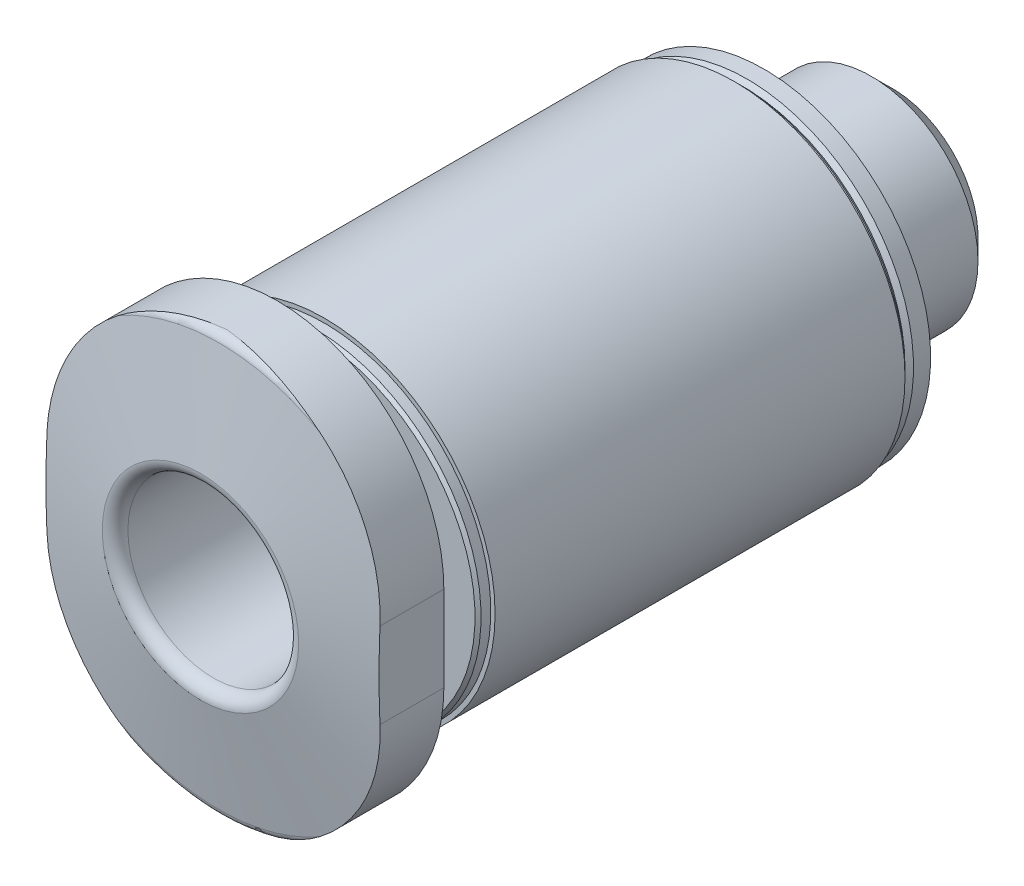
SolidWorks part; units mm, degrees
ref_plane "Front Plane" through (0, 0, 0) normal (0, 0, 1) x (1, 0, 0)
ref_plane "Top Plane" through (0, 0, 0) normal (0, 1, 0) x (1, 0, 0)
ref_plane "Right Plane" through (0, 0, 0) normal (1, 0, 0) x (0, 0, -1)
ref_plane "Plane1" through (0, 0, 0) normal (1, 0, 0) x (0, 0, -1)
sketch "Sketch1" plane through (0, 0, 0) normal (1, 0, 0) x (0, 0, -1)
  line L0 (-1.7, 0) -> (-1.7, 2)
  line L1 (-1.7, 2) -> (-12.9, 2)
  line L2 (-13.2, 2.3) -> (-12.7707, 4.7347)
  line L3 (-12.5737, 4.9) -> (-11.4, 4.9)
  line L4 (-11.4, 4.9) -> (-11.4, 3.075)
  line L5 (-11.025, 2.7) -> (-10.6, 2.7)
  line L6 (-10.6, 2.7) -> (-10.6, 3.8293)
  line L7 (-10.6, 3.8293) -> (-10.5293, 3.9)
  line L8 (-10.5293, 3.9) -> (-10.3, 3.9)
  line L9 (-10.3, 3.9) -> (-10.3, 4)
  line L10 (-10.3, 4) -> (-0.7, 4)
  line L11 (-0.7, 4) -> (-0.7, 3.9)
  line L12 (-0.7, 3.9) -> (-0.6, 3.9)
  line L13 (-0.6, 3.9) -> (-0.5, 3.8)
  line L14 (-0.5, 3.8) -> (-0.4, 3.9)
  line L15 (-0.4, 3.9) -> (0, 3.9)
  line L16 (0, 3.9) -> (0, 2.5)
  line L17 (0, 2.5) -> (2.5095, 2.5)
  line L18 (2.5095, 2.5) -> (3, 2.0095)
  line L19 (3, 2.0095) -> (3, 0)
  line L20 (3, 0) -> (-1.7, 0)
  line L21 (3, 0) -> (-1.7, 0) construction
  arc A0 (-12.9, 2) -> (-13.2, 2.3) centre (-12.9, 2.3) cw
  arc A1 (-12.7707, 4.7347) -> (-12.5737, 4.9) centre (-12.5737, 4.7) cw
  arc A2 (-11.4, 3.075) -> (-11.025, 2.7) centre (-11.025, 3.075) ccw
revolve "Revolve1" add sketch "Sketch1" angle 360 about L21
cosmetic thread "Cosmetic Thread1" parameters "D1"=3, "D2"=4.019
ref_plane "Plane2" through (0, 0, -3) normal (0, 0, 1) x (1, 0, 0)
sketch "Sketch2" plane through (0, 0, -3) normal (0, 0, 1) x (1, 0, 0)
  line L0 (-1.25, -0.7217) -> (0, -1.4434)
  line L1 (0, -1.4434) -> (1.25, -0.7217)
  line L2 (1.25, -0.7217) -> (1.25, 0.7217)
  line L3 (1.25, 0.7217) -> (0, 1.4434)
  line L4 (0, 1.4434) -> (-1.25, 0.7217)
  line L5 (-1.25, 0.7217) -> (-1.25, -0.7217)
extrude "Cut-Extrude1" cut sketch "Sketch2" along normal blind 4.7
ref_plane "Plane3" through (0, 0, 13.2) normal (0, 0, 1) x (1, 0, 0)
sketch "Sketch3" plane through (0, 0, 13.2) normal (0, 0, 1) x (1, 0, 0)
  line L0 (-10, -10) -> (10, -10)
  line L1 (10, -10) -> (10, 10)
  line L2 (10, 10) -> (-10, 10)
  line L3 (-10, 10) -> (-10, -10)
  line L4 (-3.9, 1) -> (-3.9, -1)
  line L5 (3.9, -1) -> (3.9, 1)
  arc A0 (-3.9, -1) -> (3.9, -1) centre (0, -1) ccw
  arc A1 (3.9, 1) -> (-3.9, 1) centre (0, 1) ccw
extrude "Cut-Extrude2" cut sketch "Sketch3" against normal blind 2
